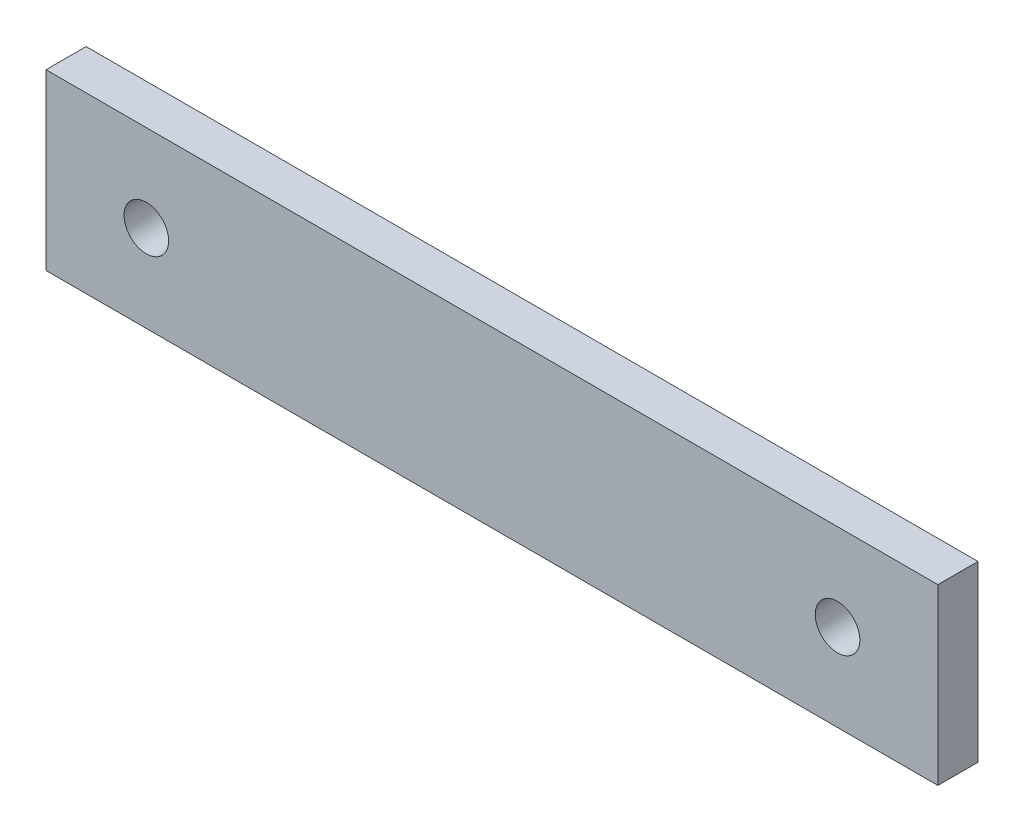
SolidWorks part; units mm, degrees
ref_plane "Plan de face" through (0, 0, 0) normal (0, 0, 1) x (1, 0, 0)
ref_plane "Plan de dessus" through (0, 0, 0) normal (0, 1, 0) x (1, 0, 0)
ref_plane "Plan de droite" through (0, 0, 0) normal (1, 0, 0) x (0, 0, -1)
sketch "Esquisse1" plane through (0, 0, 0) normal (0, 0, 1) x (1, 0, 0)
  line L0 (-43.1053, -1.3684) -> (156.8947, -1.3684) construction
  line L1 (-43.1053, 18.1316) -> (156.8947, 18.1316)
  line L2 (-43.1053, 18.1316) -> (-43.1053, -20.8684)
  line L3 (-43.1053, -20.8684) -> (156.8947, -20.8684)
  line L4 (156.8947, 18.1316) -> (156.8947, -20.8684)
  line L5 (56.8947, 18.1316) -> (56.8947, -20.8684) construction
  circle A0 centre (-20.6053, -1.3684) radius 5
  circle A1 centre (134.3947, -1.3684) radius 5
  dimension "D3" = 10
  dimension "D4" = 22.5
  dimension "D1" = 39
  dimension "D2" = 200
extrude "Boss.-Extru.1" add sketch "Esquisse1" along normal blind 9
